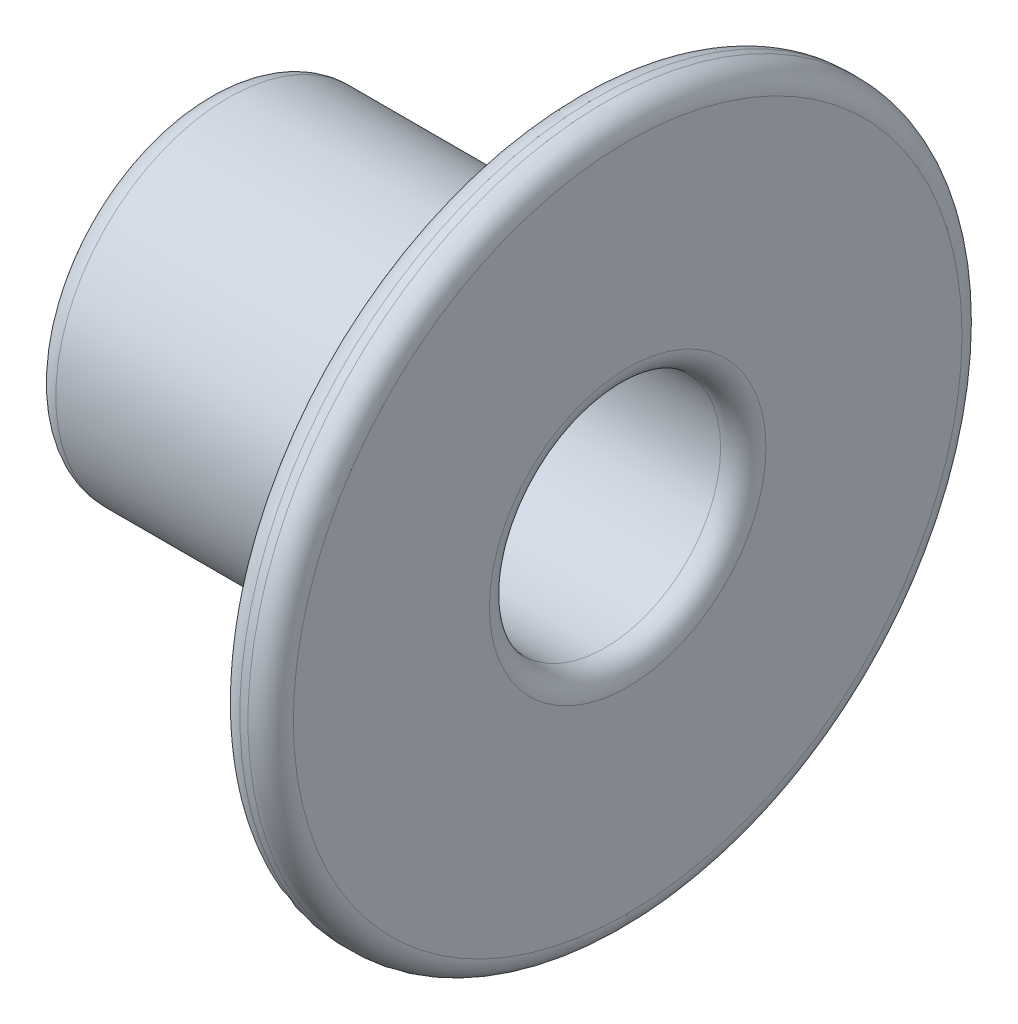
SolidWorks part; units mm, degrees
ref_plane "前视基准面" through (0, 0, 0) normal (0, 0, 1) x (1, 0, 0)
ref_plane "上视基准面" through (0, 0, 0) normal (0, 1, 0) x (1, 0, 0)
ref_plane "右视基准面" through (0, 0, 0) normal (1, 0, 0) x (0, 0, -1)
sketch "草图1" plane through (0, 0, 0) normal (0, 0, 1) x (1, 0, 0)
  line L0 (-455, 8.382) -> (-455, 0)
  line L1 (-455, 0) -> (-450, 0)
  line L2 (-450, 0) -> (-450, 6.477)
  line L3 (-450, 6.477) -> (-432.6124, 6.477)
  line L4 (-431.3424, 7.747) -> (-431.3424, 18.73)
  line L5 (-432.6124, 20) -> (-433.0724, 20)
  line L6 (-434.3424, 18.73) -> (-434.3424, 11.652)
  line L7 (-436.3424, 9.652) -> (-453.73, 9.652)
  line L8 (-455.0013, 0) -> (-431.3411, 0) construction
  arc A0 (-432.6124, 6.477) -> (-431.3424, 7.747) centre (-432.6124, 7.747) ccw
  arc A1 (-431.3424, 18.73) -> (-432.6124, 20) centre (-432.6124, 18.73) ccw
  arc A2 (-433.0724, 20) -> (-434.3424, 18.73) centre (-433.0724, 18.73) ccw
  arc A3 (-434.3424, 11.652) -> (-436.3424, 9.652) centre (-436.3424, 11.652) cw
  arc A4 (-453.73, 9.652) -> (-455, 8.382) centre (-453.73, 8.382) ccw
revolve "旋转1" add sketch "草图1" angle 360 about L8
